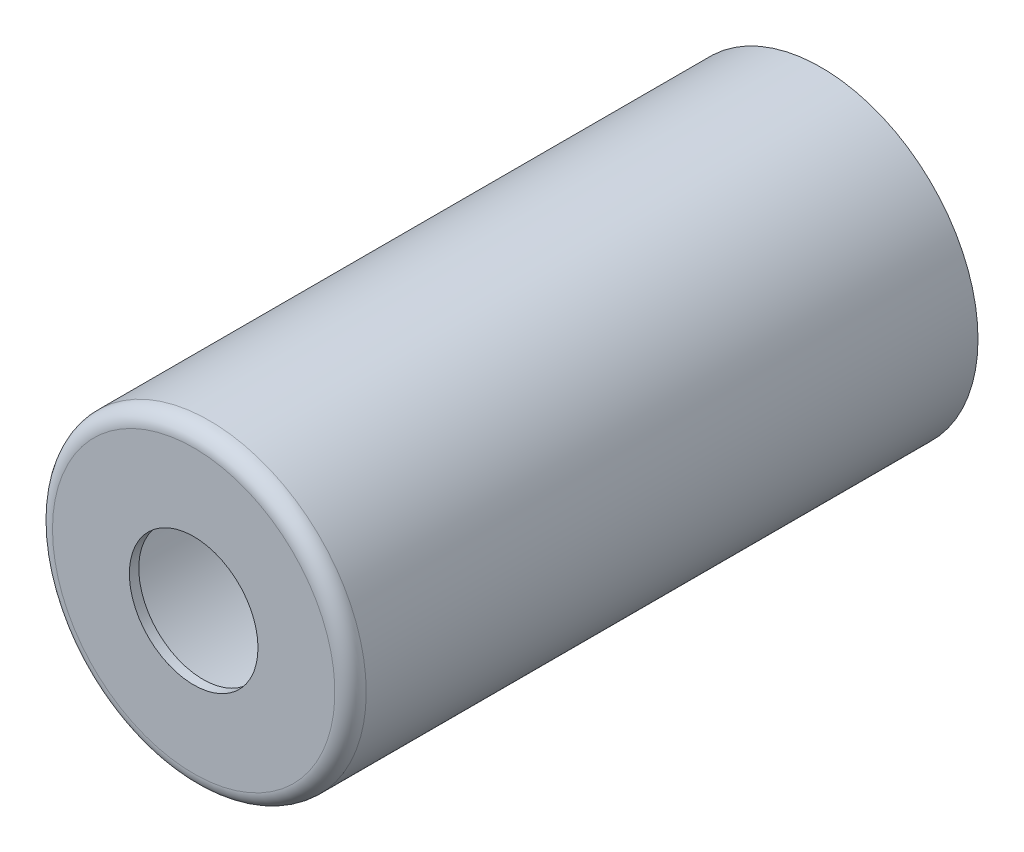
SolidWorks part; units mm, degrees
material "Стекло"
ref_plane "Front" through (0, 0, 0) normal (0, 0, 1) x (1, 0, 0)
ref_plane "Top" through (0, 0, 0) normal (0, 1, 0) x (1, 0, 0)
ref_plane "Right" through (0, 0, 0) normal (1, 0, 0) x (0, 0, -1)
sketch "Эскиз1" plane through (0, 0, 0) normal (1, 0, 0) x (0, 0, -1)
  line L0 (0, 0) -> (60.7609, 0) construction
  line L1 (0, 50) -> (0, 20.5)
  line L2 (0, 20.5) -> (3, 20.5)
  line L3 (3, 20.5) -> (3, 47)
  line L4 (3, 47) -> (200, 47)
  line L5 (200, 47) -> (200, 50)
  line L6 (200, 50) -> (0, 50)
  dimension "D1" = 100
  dimension "D2" = 100
  dimension "D3" = 200
  dimension "D4" = 41
  dimension "D5" = 3
revolve "Повернуть1" add sketch "Эскиз1" angle 360 about L0
fillet "Скругление1" radius 5 2 edges at (47, 0, -3) (50, 0, 0)
